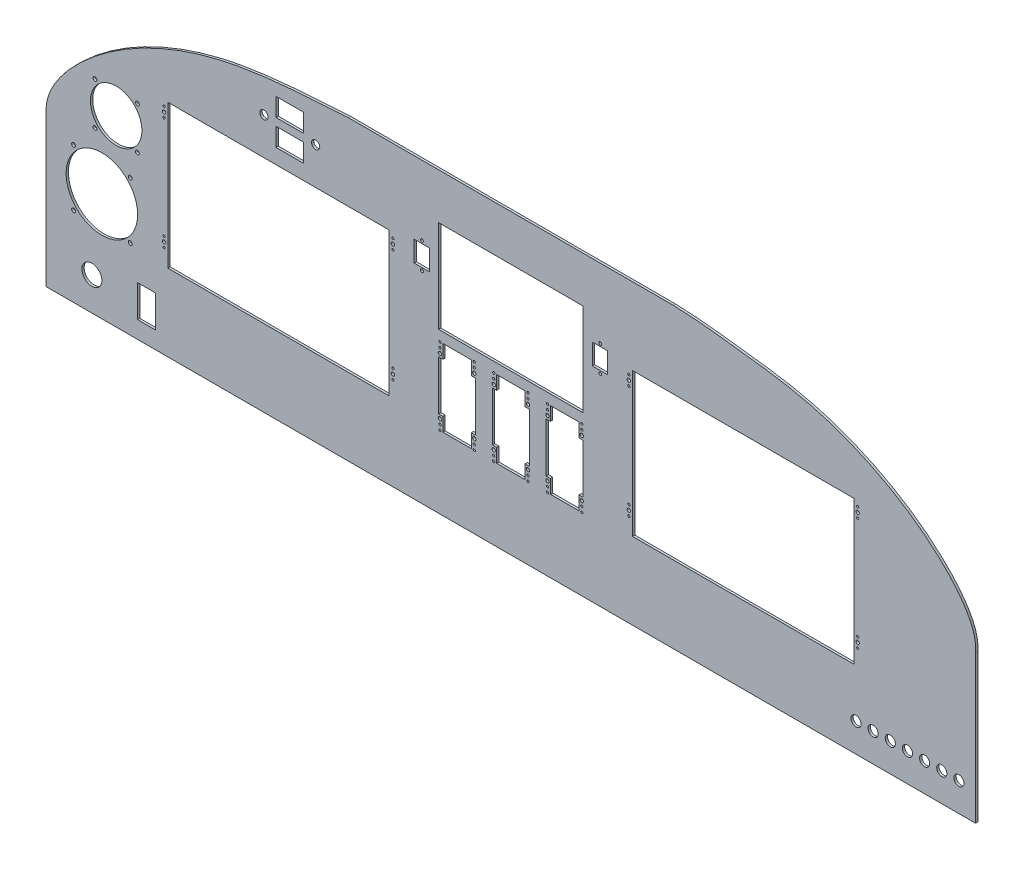
SolidWorks part; units mm, degrees
material "1060-H14"
ref_plane "Front Plane" through (0, 0, 0) normal (0, 0, 1) x (1, 0, 0)
ref_plane "Top Plane" through (0, 0, 0) normal (0, 1, 0) x (1, 0, 0)
ref_plane "Right Plane" through (0, 0, 0) normal (1, 0, 0) x (0, 0, -1)
sketch "Sketch1" plane through (0, 0, 0) normal (0, 0, 1) x (1, 0, 0)
  line L11 (-117.2518, -41.1401) -> (289.0537, -32.3757) construction
  line L16 (-166.3344, 43.9076) -> (214.5625, 52.7724) construction
  line L19 (811.9069, -110.0924) -> (-219.9681, -110.0924)
  line L20 (476.1144, 220.1076) -> (115.8244, 220.1076)
  line L21 (-219.9681, 55.0076) -> (-219.9681, -110.0924)
  line L22 (295.9694, 220.1076) -> (295.9694, -110.0924) construction
  line L23 (811.9069, 53.3694) -> (811.9069, -110.0924)
  line L24 (-199.502, -172.3599) -> (358.9513, -152.6782) construction
  line L25 (-219.2373, -92.6288) -> (285.5849, -90.9479) construction
  spline S0 degree 3 poles (115.8244, 220.1076) (89.9478, 218.3953) (43.793, 216.1258) (-34.0249, 205.3658) (-112.0591, 177.9305) (-173.6807, 135.4009) (-210.4888, 93.7245) (-221.1174, 69.3322) (-219.9681, 55.0076) knots 0 0 0 0 0.194074 0.345724 0.586619 0.805906 0.897736 1 1 1 1
  spline S2 degree 3 poles (476.1144, 220.1076) (502.1369, 219.3978) (548.0047, 213.6061) (625.995, 204.1247) (703.9836, 176.2106) (765.6162, 133.8012) (802.4299, 92.1043) (813.0587, 67.705) (811.9069, 53.3694) knots 0 0 0 0 0.194361 0.345944 0.586732 0.805923 0.897712 1 1 1 1
  point P0 (509.0496, 218.0361)
  dimension "D3" = 381
  dimension "D5" = 406.4
  dimension "D2" = 330.2
  dimension "D4" = 515.9375
  dimension "D6" = 1031.875
  dimension "D7" = 165.1
  dimension "D8" = 558.8
  dimension "D9" = 504.825
extrude "Boss-Extrude1" add sketch "Sketch1" along normal blind 2.54
sketch "Cutouts" plane through (0, 0, 2.54) normal (0, 0, 1) x (1, 0, 0)
  line L0 (57.1239, -14.1451) -> (223.9618, -14.1451) construction
  line L11 (550.6278, 1448.8605) -> (3233.1045, 1448.8605) construction
  line L12 (223.9618, -14.1451) -> (223.9618, 222.0749) construction
  line L13 (-162.1683, 45.1669) -> (244.1923, 50.8314) construction
  line L18 (-530.8086, 186.32) -> (-473.1506, 186.32) construction
  line L19 (-530.8086, 186.32) -> (-530.8086, 128.662) construction
  line L21 (-473.1506, 186.32) -> (-473.1506, 128.662) construction
  line L23 (-521.8907, 186.32) -> (-530.8086, 177.4022)
  line L25 (-482.0684, 186.32) -> (-473.1506, 177.4022)
  line L27 (-473.1506, 137.5799) -> (-482.0684, 128.662)
  line L29 (-530.8086, 137.5799) -> (-521.8907, 128.662)
  line L31 (-521.8907, 186.32) -> (-530.8086, 186.32)
  line L34 (-530.8086, 177.4022) -> (-530.8086, 137.5799)
  line L36 (-521.8907, 128.662) -> (-482.0684, 128.662)
  line L38 (-473.1506, 137.5799) -> (-473.1506, 177.4022)
  line L40 (-482.0684, 186.32) -> (-521.8907, 186.32)
  line L43 (-473.1506, 177.4022) -> (-473.1506, 186.32)
  line L44 (-473.1506, 186.32) -> (-482.0684, 186.32)
  line L46 (-521.8907, 186.32) -> (-530.8086, 186.32)
  line L48 (-530.8086, 177.4022) -> (-530.8086, 186.32)
  line L49 (-530.8086, 137.5799) -> (-530.8086, 128.662)
  line L50 (-530.8086, 128.662) -> (-521.8907, 128.662)
  line L51 (-473.1506, 137.5799) -> (-473.1506, 128.662)
  line L52 (-482.0684, 128.662) -> (-473.1506, 128.662)
  line L53 (188.448, 139.8436) -> (178.3356, 139.8436) construction
  line L54 (205.593, 139.8436) -> (215.7054, 139.8436) construction
  line L55 (-219.9681, -110.0924) -> (811.9069, -110.0924) construction
  line L58 (35.2637, 180.1457) -> (65.7437, 180.1457)
  line L59 (35.2637, 180.1457) -> (35.2637, 200.4657)
  line L60 (35.2637, 200.4657) -> (65.7437, 200.4657)
  line L61 (65.7437, 180.1457) -> (65.7437, 200.4657)
  line L62 (215.7054, 135.2716) -> (376.2334, 135.2716)
  line L63 (35.2637, 171.6953) -> (65.7437, 171.6953)
  line L64 (35.2637, 171.6953) -> (35.2637, 151.3753)
  line L65 (35.2637, 151.3753) -> (65.7437, 151.3753)
  line L66 (65.7437, 171.6953) -> (65.7437, 151.3753)
  line L67 (215.7054, 135.2716) -> (215.7054, 66.6916)
  line L68 (215.7054, 66.6916) -> (376.2334, 66.6916)
  line L75 (-142.2274, 93.1076) -> (-118.6543, 116.6807) construction
  line L79 (376.2334, 135.2716) -> (376.2334, 66.6916)
  line L85 (-219.9681, 55.0076) -> (-219.9681, -110.0924) construction
  line L86 (215.7054, 169.3076) -> (376.2334, 169.3076)
  line L89 (-142.2274, 93.1076) -> (-165.8006, 69.5344) construction
  line L90 (295.9694, -110.0924) -> (295.9694, 220.1076) construction
  line L91 (-118.3681, -55.4824) -> (-98.5561, -55.4824)
  line L92 (-118.3681, -55.4824) -> (-118.3681, -91.0424)
  line L93 (-118.3681, -91.0424) -> (-98.5561, -91.0424)
  line L94 (-98.5561, -55.4824) -> (-98.5561, -91.0424)
  line L102 (215.7054, 169.3076) -> (215.7054, 136.5416)
  line L105 (215.7054, 66.6916) -> (376.2334, 66.6916)
  line L106 (21.7703, 175.9205) -> (35.2637, 175.9205) construction
  line L107 (79.2371, 175.9205) -> (65.7437, 175.9205) construction
  line L111 (476.1144, 220.1076) -> (115.8244, 220.1076) construction
  line L114 (35.2637, 180.1457) -> (35.2637, 171.6953) construction
  line L115 (215.7054, 136.5416) -> (376.2334, 136.5416)
  line L116 (376.2334, 169.3076) -> (376.2334, 136.5416)
  line L138 (215.7054, 66.6916) -> (215.7054, 169.3076)
  line L139 (215.7054, 169.3076) -> (376.2334, 169.3076)
  line L140 (376.2334, 66.6916) -> (376.2334, 169.3076)
  line L141 (386.3458, 139.8436) -> (376.2334, 139.8436) construction
  line L146 (742.5331, -84.4384) -> (742.5331, 54.9956) construction
  line L150 (403.4908, 139.8436) -> (413.6031, 139.8436) construction
  circle A35 centre (-169.1681, -73.2624) radius 11.1125
  circle A37 centre (21.7703, 175.9205) radius 4.572
  circle A44 centre (-529.2846, 184.796) radius 1.8288
  circle A46 centre (-474.6746, 184.796) radius 1.8288
  circle A47 centre (-474.6746, 130.186) radius 1.8288
  circle A48 centre (-529.2846, 130.186) radius 1.8288
  circle A51 centre (79.2371, 175.9205) radius 4.572
  circle A53 centre (-118.6543, 69.5344) radius 2.159
  circle A54 centre (-165.8006, 69.5344) radius 2.159
  circle A55 centre (-165.8006, 116.6807) radius 2.159
  circle A56 centre (-118.6543, 116.6807) radius 2.159
  circle A57 centre (-142.2274, 93.1076) radius 28.575
  circle A64 centre (-651.5272, 104.7302) radius 40.005
  circle A65 centre (679.0947, -78.3424) radius 5.6515
  circle A66 centre (698.1447, -78.3424) radius 5.6515
  circle A67 centre (717.1947, -78.3424) radius 5.6515
  circle A68 centre (736.2447, -78.3424) radius 5.6515
  circle A69 centre (755.2947, -78.3424) radius 5.6515
  circle A70 centre (774.3447, -78.3424) radius 5.6515
  circle A71 centre (793.3947, -78.3424) radius 5.6515
  point P16 (-139.867, 149.4505)
  point P31 (-501.9796, 186.32)
  point P66 (295.9694, 55.5156)
  point P75 (295.9694, 55.0076)
  point P80 (679.0947, -78.3424)
  point P81 (698.1447, -78.3424)
  point P82 (717.1947, -78.3424)
  point P83 (736.2447, -78.3424)
  point P84 (755.2947, -78.3424)
  point P85 (774.3447, -78.3424)
  point P86 (295.9694, 169.3076)
  point P87 (0, 0)
  point P89 (-118.3681, -73.2624)
  point P105 (793.3947, -78.3424)
  point P108 (0, 0)
  point P109 (35.2637, 175.9205)
  point P114 (-165.8006, 69.5344)
  line B0 (197.2987, 142.8535) -> (197.2987, 139.8436) construction
  line B1 (188.448, 139.8436) -> (205.593, 139.8436)
  line B2 (188.448, 139.8436) -> (188.448, 116.8566)
  line B3 (188.448, 116.8566) -> (205.593, 116.8566)
  line B4 (205.593, 139.8436) -> (205.593, 116.8566)
  line B5 (197.2987, 113.8467) -> (197.2987, 116.8566) construction
  circle B6 centre (197.2987, 142.8535) radius 1.6319
  circle B7 centre (197.2987, 113.8467) radius 1.6319
  line B8 (-87.0944, 123.3336) -> (-84.9354, 123.3336) construction
  line B9 (-84.9354, 134.7636) -> (160.9366, 134.7636)
  line B10 (-84.9354, 134.7636) -> (-84.9354, -24.7484)
  line B11 (-84.9354, -24.7484) -> (160.9366, -24.7484)
  line B12 (160.9366, 134.7636) -> (160.9366, -24.7484)
  line B13 (163.0956, 123.3336) -> (160.9366, 123.3336) construction
  line B14 (-88.9994, 128.8836) -> (-88.9994, 123.3336) construction
  line B15 (-88.9994, 123.3336) -> (-88.9994, 117.7836) construction
  line B16 (-88.9994, 117.7836) -> (-88.9994, 123.3336)
  line B17 (-88.9994, 3.9156) -> (-88.9994, -1.6344) construction
  line B18 (-88.9994, -1.6344) -> (-88.9994, -7.1844) construction
  line B19 (-88.9994, -7.1844) -> (-88.9994, -1.6344)
  line B20 (-102.3344, -29.8284) -> (-102.3344, 139.8436) construction
  line B21 (-102.3344, 139.8436) -> (178.3356, 139.8436) construction
  line B22 (178.3356, 139.8436) -> (178.3356, -29.8284) construction
  line B23 (178.3356, -29.8284) -> (-102.3344, -29.8284) construction
  line B24 (38.3785, 123.3336) -> (40.5375, 123.3336) construction
  line B25 (165.0006, 128.8836) -> (165.0006, 123.3336) construction
  line B26 (165.0006, 123.3336) -> (165.0006, 117.7836) construction
  line B27 (165.0006, 117.7836) -> (165.0006, 123.3336) construction
  line B28 (37.7673, -1.6344) -> (39.9263, -1.6344) construction
  line B29 (165.0006, 3.9156) -> (165.0006, -1.6344) construction
  line B30 (165.0006, -1.6344) -> (165.0006, -7.1844) construction
  line B31 (165.0006, -7.1844) -> (165.0006, -1.6344)
  circle B32 centre (165.0006, 123.3336) radius 1.905
  circle B33 centre (-88.9994, 123.3336) radius 1.905
  circle B34 centre (-88.9994, -1.6344) radius 1.905
  circle B35 centre (165.0006, -1.6344) radius 1.905
  circle B36 centre (-88.9994, 128.8836) radius 1.2446
  circle B37 centre (-88.9994, 117.7836) radius 1.2446
  circle B38 centre (-88.9994, 3.9156) radius 1.2446
  circle B39 centre (-88.9994, -7.1844) radius 1.2446
  circle B40 centre (165.0006, 128.8836) radius 1.2446
  circle B41 centre (165.0006, 117.7836) radius 1.2446
  circle B42 centre (165.0006, 3.9156) radius 1.2446
  circle B43 centre (165.0006, -7.1844) radius 1.2446
  line B44 (-433.1322, 87.1552) -> (-350.5822, 87.1552)
  line B45 (-433.1322, 87.1552) -> (-433.1322, 36.3552)
  line B46 (-433.1322, 36.3552) -> (-350.5822, 36.3552)
  line B47 (-350.5822, 87.1552) -> (-350.5822, 36.3552)
  circle B48 centre (-126.6468, -21.4806) radius 2.159
  circle B49 centre (-158.0793, 9.9519) radius 39.6875
  circle B50 centre (-189.5118, -21.4806) radius 2.159
  circle B51 centre (-126.6468, 41.3844) radius 2.159
  circle B52 centre (-189.5118, 41.3844) radius 2.159
  line B53 (311.7174, -29.8284) -> (280.2214, -29.8284)
  line B54 (311.7174, -29.8284) -> (311.7174, -14.5884)
  line B55 (311.7174, -14.5884) -> (316.5434, -14.5884)
  line B56 (316.5434, -14.5884) -> (316.5434, 40.2756)
  line B57 (316.5434, 40.2756) -> (311.7174, 40.2756)
  line B58 (311.7174, 40.2756) -> (311.7174, 55.5156)
  line B59 (311.7174, 55.5156) -> (280.2214, 55.5156)
  line B60 (280.2214, 55.5156) -> (280.2214, 40.2756)
  line B61 (280.2214, 40.2756) -> (275.3954, 40.2756)
  line B62 (275.3954, 40.2756) -> (275.3954, -14.5884)
  line B63 (275.3954, -14.5884) -> (280.2214, -14.5884)
  line B64 (280.2214, -14.5884) -> (280.2214, -29.8284)
  line B65 (276.9194, -16.6458) -> (276.9194, -14.5884) construction
  line B66 (315.0194, -17.8392) -> (315.0194, -15.7818) construction
  circle B67 centre (315.0194, 44.238) radius 1.905
  circle B68 centre (276.9194, -18.5508) radius 1.905
  circle B69 centre (315.0194, -18.5508) radius 1.905
  circle B70 centre (315.0194, 49.7752) radius 1.2192
  circle B71 centre (315.0194, 55.3378) radius 1.2192
  circle B72 centre (276.9194, 44.238) radius 1.905
  circle B73 centre (276.9194, 49.7752) radius 1.2192
  circle B74 centre (276.9194, 55.3378) radius 1.2192
  circle B75 centre (276.9194, -24.088) radius 1.2192
  circle B76 centre (276.9194, -29.6506) radius 1.2192
  circle B77 centre (315.0194, -24.088) radius 1.2192
  circle B78 centre (315.0194, -29.6506) radius 1.2192
  line B79 (252.0274, -29.8284) -> (220.5314, -29.8284)
  line B80 (252.0274, -29.8284) -> (252.0274, -14.5884)
  line B81 (252.0274, -14.5884) -> (256.8534, -14.5884)
  line B82 (256.8534, -14.5884) -> (256.8534, 40.2756)
  line B83 (256.8534, 40.2756) -> (252.0274, 40.2756)
  line B84 (252.0274, 40.2756) -> (252.0274, 55.5156)
  line B85 (252.0274, 55.5156) -> (220.5314, 55.5156)
  line B86 (220.5314, 55.5156) -> (220.5314, 40.2756)
  line B87 (220.5314, 40.2756) -> (215.7054, 40.2756)
  line B88 (215.7054, 40.2756) -> (215.7054, -14.5884)
  line B89 (215.7054, -14.5884) -> (220.5314, -14.5884)
  line B90 (220.5314, -14.5884) -> (220.5314, -29.8284)
  line B91 (217.2294, -16.6458) -> (217.2294, -14.5884) construction
  line B92 (255.3294, -17.8392) -> (255.3294, -15.7818) construction
  circle B93 centre (255.3294, 44.238) radius 1.905
  circle B94 centre (217.2294, -18.5508) radius 1.905
  circle B95 centre (255.3294, -18.5508) radius 1.905
  circle B96 centre (255.3294, 49.7752) radius 1.2192
  circle B97 centre (255.3294, 55.3378) radius 1.2192
  circle B98 centre (217.2294, 44.238) radius 1.905
  circle B99 centre (217.2294, 49.7752) radius 1.2192
  circle B100 centre (217.2294, 55.3378) radius 1.2192
  circle B101 centre (217.2294, -24.088) radius 1.2192
  circle B102 centre (217.2294, -29.6506) radius 1.2192
  circle B103 centre (255.3294, -24.088) radius 1.2192
  circle B104 centre (255.3294, -29.6506) radius 1.2192
  line B105 (428.8431, 123.3336) -> (431.0021, 123.3336) construction
  line B106 (431.0021, 134.7636) -> (676.8741, 134.7636)
  line B107 (431.0021, 134.7636) -> (431.0021, -24.7484)
  line B108 (431.0021, -24.7484) -> (676.8741, -24.7484)
  line B109 (676.8741, 134.7636) -> (676.8741, -24.7484)
  line B110 (679.0331, 123.3336) -> (676.8741, 123.3336) construction
  line B111 (426.9381, 128.8836) -> (426.9381, 123.3336) construction
  line B112 (426.9381, 123.3336) -> (426.9381, 117.7836) construction
  line B113 (426.9381, 117.7836) -> (426.9381, 123.3336)
  line B114 (426.9381, 3.9156) -> (426.9381, -1.6344) construction
  line B115 (426.9381, -1.6344) -> (426.9381, -7.1844) construction
  line B116 (426.9381, -7.1844) -> (426.9381, -1.6344)
  line B117 (413.6031, -29.8284) -> (413.6031, 139.8436) construction
  line B118 (413.6031, 139.8436) -> (694.2731, 139.8436) construction
  line B119 (694.2731, 139.8436) -> (694.2731, -29.8284) construction
  line B120 (694.2731, -29.8284) -> (413.6031, -29.8284) construction
  line B121 (554.316, 123.3336) -> (556.475, 123.3336) construction
  line B122 (680.9381, 128.8836) -> (680.9381, 123.3336) construction
  line B123 (680.9381, 123.3336) -> (680.9381, 117.7836) construction
  line B124 (680.9381, 117.7836) -> (680.9381, 123.3336) construction
  line B125 (553.7048, -1.6344) -> (555.8638, -1.6344) construction
  line B126 (680.9381, 3.9156) -> (680.9381, -1.6344) construction
  line B127 (680.9381, -1.6344) -> (680.9381, -7.1844) construction
  line B128 (680.9381, -7.1844) -> (680.9381, -1.6344)
  circle B129 centre (680.9381, 123.3336) radius 1.905
  circle B130 centre (426.9381, 123.3336) radius 1.905
  circle B131 centre (426.9381, -1.6344) radius 1.905
  circle B132 centre (680.9381, -1.6344) radius 1.905
  circle B133 centre (426.9381, 128.8836) radius 1.2446
  circle B134 centre (426.9381, 117.7836) radius 1.2446
  circle B135 centre (426.9381, 3.9156) radius 1.2446
  circle B136 centre (426.9381, -7.1844) radius 1.2446
  circle B137 centre (680.9381, 128.8836) radius 1.2446
  circle B138 centre (680.9381, 117.7836) radius 1.2446
  circle B139 centre (680.9381, 3.9156) radius 1.2446
  circle B140 centre (680.9381, -7.1844) radius 1.2446
  line B141 (395.1965, 142.8535) -> (395.1965, 139.8436) construction
  line B142 (386.3458, 139.8436) -> (403.4908, 139.8436)
  line B143 (386.3458, 139.8436) -> (386.3458, 116.8566)
  line B144 (386.3458, 116.8566) -> (403.4908, 116.8566)
  line B145 (403.4908, 139.8436) -> (403.4908, 116.8566)
  line B146 (395.1965, 113.8467) -> (395.1965, 116.8566) construction
  circle B147 centre (395.1965, 142.8535) radius 1.6319
  circle B148 centre (395.1965, 113.8467) radius 1.6319
  line B149 (371.4074, -29.8284) -> (339.9114, -29.8284)
  line B150 (371.4074, -29.8284) -> (371.4074, -14.5884)
  line B151 (371.4074, -14.5884) -> (376.2334, -14.5884)
  line B152 (376.2334, -14.5884) -> (376.2334, 40.2756)
  line B153 (376.2334, 40.2756) -> (371.4074, 40.2756)
  line B154 (371.4074, 40.2756) -> (371.4074, 55.5156)
  line B155 (371.4074, 55.5156) -> (339.9114, 55.5156)
  line B156 (339.9114, 55.5156) -> (339.9114, 40.2756)
  line B157 (339.9114, 40.2756) -> (335.0854, 40.2756)
  line B158 (335.0854, 40.2756) -> (335.0854, -14.5884)
  line B159 (335.0854, -14.5884) -> (339.9114, -14.5884)
  line B160 (339.9114, -14.5884) -> (339.9114, -29.8284)
  line B161 (336.6094, -16.6458) -> (336.6094, -14.5884) construction
  line B162 (374.7094, -17.8392) -> (374.7094, -15.7818) construction
  circle B163 centre (374.7094, 44.238) radius 1.905
  circle B164 centre (336.6094, -18.5508) radius 1.905
  circle B165 centre (374.7094, -18.5508) radius 1.905
  circle B166 centre (374.7094, 49.7752) radius 1.2192
  circle B167 centre (374.7094, 55.3378) radius 1.2192
  circle B168 centre (336.6094, 44.238) radius 1.905
  circle B169 centre (336.6094, 49.7752) radius 1.2192
  circle B170 centre (336.6094, 55.3378) radius 1.2192
  circle B171 centre (336.6094, -24.088) radius 1.2192
  circle B172 centre (336.6094, -29.6506) radius 1.2192
  circle B173 centre (374.7094, -24.088) radius 1.2192
  circle B174 centre (374.7094, -29.6506) radius 1.2192
  dimension "D3" = 20.32
  dimension "D4" = 30.48
  dimension "D5" = 22.225
  dimension "D6" = 9.144
  dimension "D8" = 57.658
  dimension "D9" = 57.658
  dimension "D10" = 3.6576
  dimension "D14" = 1.524
  dimension "D15" = 8.9178
  dimension "D16" = 9.144
  dimension "D17" = 31.75
  dimension "D28" = 135.0327
  dimension "D29" = 1.27
  dimension "D30" = 19.05
  dimension "D31" = 19.05
  dimension "D32" = 19.05
  dimension "D33" = 19.05
  dimension "D39" = 19.05
  dimension "D40" = 160.528
  dimension "D41" = 203.2
  dimension "D7" = 47.1463
  dimension "D12" = 54.61
  dimension "D20" = 48.26
  dimension "D21" = 4.318
  dimension "D24" = 57.15
  dimension "D34" = 80.01
  dimension "D35" = 11.303
  dimension "D36" = 19.05
  dimension "D2" = 406.4
  dimension "D11" = 54.61
  dimension "D13" = 27.305
  dimension "D18" = 19.05
  dimension "D19" = 47.1463
  dimension "D22" = 19.812
  dimension "D23" = 50.8
  dimension "D25" = 35.56
  dimension "D26" = 50.8
  dimension "D27" = 135.0328
  dimension "D37" = 68.58
  dimension "D42" = 101.6
  dimension "D45" = 32.766
sketch_block_instance "USB Block-1"
sketch_block "USB Block" parameters "D3"=3.2639, "D1"=17.145, "D2"=22.987, "D4"=3.0099, "D5"=8.2943
sketch_block_instance "HDX Block-1"
sketch_block "HDX Block" parameters "D1"=3.81, "D11"=2.4892, "D13"=2.4892, "D15"=2.4892, "D18"=2.4892, "D2"=124.968, "D3"=11.43, "D4"=159.512, "D5"=245.872, "D6"=254, "D7"=280.67, "D8"=169.672, "D9"=5.08, "D10"=17.399, "D12"=11.1, "D14"=11.1, "D16"=11.1, "D17"=5.55, "D19"=11.1, "D20"=5.55, "D21"=5.08
sketch_block_instance "Electroair-1"
sketch_block "Electroair" parameters "D1"=82.55, "D2"=50.8
sketch_block_instance "Standard Inst-1"
sketch_block "Standard Inst" parameters "D1"=79.375
sketch_block_instance "Button Panel-5"
sketch_block "Button Panel" parameters "D7"=2.4384, "D14"=3.81, "D1"=85.344, "D2"=31.496, "D3"=38.1, "D4"=62.7888, "D5"=5.5372, "D6"=5.5626, "D8"=5.5372, "D9"=5.5626, "D10"=5.5372, "D11"=5.5372, "D12"=4.826, "D13"=3.302
sketch_block_instance "Button Panel-6"
sketch_block_instance "HDX Block-4"
sketch_block_instance "USB Block-2"
sketch_block_instance "Button Panel-7"
extrude "Cut-Extrude2" cut sketch "Cutouts" against normal blind 35.56
